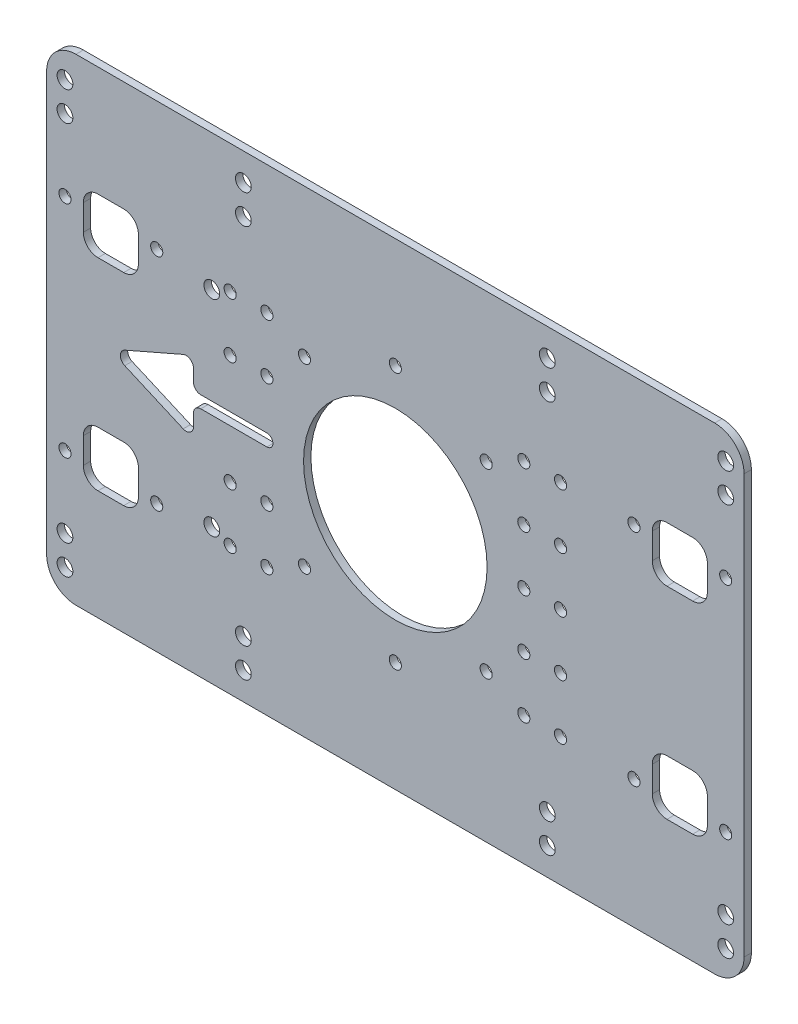
SolidWorks part; units mm, degrees
ref_plane "前视基准面" through (0, 0, 0) normal (0, 0, 1) x (1, 0, 0)
ref_plane "上视基准面" through (0, 0, 0) normal (0, 1, 0) x (1, 0, 0)
ref_plane "右视基准面" through (0, 0, 0) normal (1, 0, 0) x (0, 0, -1)
sketch "草图1" plane through (0, 0, 0) normal (0, 0, 1) x (1, 0, 0)
  line L0 (0, 65) -> (190, 65) construction
  line L1 (0, 0) -> (190, 0)
  line L2 (0, 0) -> (0, 130)
  line L3 (0, 130) -> (190, 130)
  line L4 (190, 0) -> (190, 130)
  line L5 (95, 130) -> (95, 0) construction
  line L6 (0, 0) -> (190, 0)
  line L7 (0, 130) -> (190, 130)
  circle A0 centre (5, 7.5) radius 2.15
  circle A1 centre (53.6, 7.5) radius 2.15
  circle A2 centre (53.6, 15.5) radius 2.15
  circle A3 centre (5, 15.5) radius 2.15
  circle A4 centre (5, 114.5) radius 2.15
  circle A5 centre (53.6, 122.5) radius 2.15
  circle A6 centre (5, 122.5) radius 2.15
  circle A7 centre (53.6, 114.5) radius 2.15
  circle A8 centre (53.6, 7.5) radius 2.15
  circle A9 centre (5, 7.5) radius 2.15
  circle A10 centre (5, 15.5) radius 2.15
  circle A11 centre (5, 114.5) radius 2.15
  circle A12 centre (53.6, 114.5) radius 2.15
  circle A13 centre (53.6, 122.5) radius 2.15
  circle A14 centre (5, 122.5) radius 2.15
  circle A15 centre (185, 122.5) radius 2.15
  circle A16 centre (136.4, 122.5) radius 2.15
  circle A17 centre (136.4, 114.5) radius 2.15
  circle A18 centre (185, 114.5) radius 2.15
  circle A19 centre (185, 15.5) radius 2.15
  circle A20 centre (185, 7.5) radius 2.15
  circle A21 centre (136.4, 7.5) radius 2.15
  circle A22 centre (136.4, 114.5) radius 2.15
  circle A23 centre (185, 122.5) radius 2.15
  circle A24 centre (136.4, 122.5) radius 2.15
  circle A25 centre (185, 114.5) radius 2.15
  circle A26 centre (185, 15.5) radius 2.15
  circle A27 centre (136.4, 15.5) radius 2.15
  circle A28 centre (136.4, 7.5) radius 2.15
  circle A29 centre (185, 7.5) radius 2.15
  dimension "D4" = 4.3
  dimension "D3" = 7.5
  dimension "D5" = 48.6
  dimension "D6" = 5
  dimension "D7" = 190
  dimension "D8" = 130
  dimension "D9" = 8
  dimension "D1" = 2
  dimension "D2" = 2
extrude "凸台-拉伸1" add sketch "草图1" along normal blind 2 contours L1 L4 L3 L2 A21 A19 A18 A17 A16 A15 A6 A4 A3 A2 A1 A0 A5 A7 A20 A27
fillet "圆角1" radius 8 4 edges at (0, 130, 1) (190, 130, 1) (190, 0, 1) (0, 0, 1)
sketch "草图2" plane through (0, 0, 0) normal (0, 0, -1) x (-1, 0, 0)
  line L0 (-95, 0) -> (-95, 130) construction
  line L1 (-190, 65) -> (0, 65) construction
  line L2 (-21, 85) -> (-14, 85)
  line L3 (-21, 30) -> (-14, 30)
  line L4 (0, 8) -> (0, 122)
  line L5 (-8, 130) -> (-182, 130)
  line L6 (-190, 122) -> (-190, 8)
  line L7 (-182, 0) -> (-8, 0)
  line L8 (0, 8) -> (0, 122)
  line L9 (-8, 130) -> (-182, 130)
  line L10 (-190, 122) -> (-190, 8)
  line L11 (-182, 0) -> (-8, 0)
  line L12 (-25, 34) -> (-25, 41)
  line L13 (-21, 45) -> (-14, 45)
  line L14 (-10, 34) -> (-10, 41)
  line L15 (-10, 96) -> (-10, 89)
  line L16 (-21, 100) -> (-14, 100)
  line L17 (-25, 96) -> (-25, 89)
  line L18 (-165, 96) -> (-165, 89)
  line L19 (-169, 100) -> (-176, 100)
  line L20 (-180, 96) -> (-180, 89)
  line L21 (-169, 85) -> (-176, 85)
  line L22 (-169, 45) -> (-176, 45)
  line L23 (-180, 34) -> (-180, 41)
  line L24 (-169, 30) -> (-176, 30)
  line L25 (-165, 34) -> (-165, 41)
  arc A0 (-14, 45) -> (-10, 41) centre (-14, 41) cw
  arc A1 (-25, 41) -> (-21, 45) centre (-21, 41) cw
  arc A2 (-10, 34) -> (-14, 30) centre (-14, 34) cw
  arc A3 (-21, 30) -> (-25, 34) centre (-21, 34) cw
  arc A4 (0, 122) -> (-8, 130) centre (-8, 122) ccw
  arc A5 (-182, 130) -> (-190, 122) centre (-182, 122) ccw
  arc A6 (-190, 8) -> (-182, 0) centre (-182, 8) ccw
  arc A7 (-8, 0) -> (0, 8) centre (-8, 8) ccw
  arc A8 (0, 122) -> (-8, 130) centre (-8, 122) ccw
  arc A9 (-182, 130) -> (-190, 122) centre (-182, 122) ccw
  arc A10 (-190, 8) -> (-182, 0) centre (-182, 8) ccw
  arc A11 (-8, 0) -> (0, 8) centre (-8, 8) ccw
  arc A12 (-14, 85) -> (-10, 89) centre (-14, 89) ccw
  arc A13 (-10, 96) -> (-14, 100) centre (-14, 96) ccw
  arc A14 (-25, 89) -> (-21, 85) centre (-21, 89) ccw
  arc A15 (-21, 100) -> (-25, 96) centre (-21, 96) ccw
  arc A16 (-165, 89) -> (-169, 85) centre (-169, 89) cw
  arc A17 (-169, 100) -> (-165, 96) centre (-169, 96) cw
  arc A18 (-180, 96) -> (-176, 100) centre (-176, 96) cw
  arc A19 (-176, 85) -> (-180, 89) centre (-176, 89) cw
  arc A20 (-176, 45) -> (-180, 41) centre (-176, 41) ccw
  arc A21 (-180, 34) -> (-176, 30) centre (-176, 34) ccw
  arc A22 (-165, 41) -> (-169, 45) centre (-169, 41) ccw
  arc A23 (-169, 30) -> (-165, 34) centre (-169, 34) ccw
  circle A24 centre (-95, 65) radius 25
  dimension "D2" = 4
  dimension "D7" = 50
  dimension "D3" = 15
  dimension "D4" = 15
  dimension "D5" = 30
  dimension "D6" = 10
  dimension "D8" = 0
  dimension "D1" = 0
extrude "切除-拉伸1" cut sketch "草图2" against normal blind 10 contours A24 | L12 A1 L13 A0 L14 A2 L3 A3 | L2 A12 L15 A13 L16 A15 L17 A14 | A16 L21 A19 L20 A18 L19 A17 L18 | L22 A20 L23 A21 L24 A23 L25 A22
sketch "草图4" plane through (0, 0, 0) normal (0, 0, -1) x (-1, 0, 0)
  line L0 (0, 65) -> (-60, 65)
  line L1 (-60, 65) -> (-40, 65) construction
  line L2 (-60, 66.65) -> (-40, 66.65)
  line L3 (-60, 63.35) -> (-40, 63.35)
  line L4 (0, 8) -> (0, 122)
  line L5 (-8, 130) -> (-182, 130)
  line L6 (-190, 122) -> (-190, 8)
  line L7 (-182, 0) -> (-8, 0)
  line L8 (0, 8) -> (0, 122)
  line L9 (-8, 130) -> (-182, 130)
  line L10 (-190, 122) -> (-190, 8)
  line L11 (-182, 0) -> (-8, 0)
  line L12 (-40, 75) -> (-40, 55)
  line L13 (-40, 55) -> (-17.0871, 65)
  line L14 (-40, 75) -> (-17.0871, 65)
  arc A0 (-60, 66.65) -> (-60, 63.35) centre (-60, 65) ccw
  arc A1 (-40, 63.35) -> (-40, 66.65) centre (-40, 65) ccw
  arc A4 (0, 122) -> (-8, 130) centre (-8, 122) ccw
  arc A5 (-182, 130) -> (-190, 122) centre (-182, 122) ccw
  arc A6 (-190, 8) -> (-182, 0) centre (-182, 8) ccw
  arc A7 (-8, 0) -> (0, 8) centre (-8, 8) ccw
  arc A8 (0, 122) -> (-8, 130) centre (-8, 122) ccw
  arc A9 (-182, 130) -> (-190, 122) centre (-182, 122) ccw
  arc A10 (-190, 8) -> (-182, 0) centre (-182, 8) ccw
  arc A11 (-8, 0) -> (0, 8) centre (-8, 8) ccw
  point P12 (-50, 65)
  point P22 (0, 0)
  point P25 (-40, 65)
  dimension "D3" = 1.65
  dimension "D2" = 20
  dimension "D4" = 10
  dimension "D5" = 25
  dimension "D7" = 60
  dimension "D1" = 0
extrude "切除-拉伸2" cut sketch "草图4" against normal blind 10
fillet "圆角2" radius 2 5 edges at (17.0871, 65, 1) (40, 63.35, 1) (40, 75, 1) (40, 55, 1) (40, 66.65, 1)
sketch "草图5" plane through (0, 0, 0) normal (0, 0, -1) x (-1, 0, 0)
  line L0 (-190, 65) -> (-129.7774, 65) construction
  line L4 (0, 8) -> (0, 122)
  line L5 (-8, 130) -> (-182, 130)
  line L6 (-190, 122) -> (-190, 8)
  line L7 (-182, 0) -> (-8, 0)
  line L8 (0, 8) -> (0, 122)
  line L9 (-8, 130) -> (-182, 130)
  line L10 (-190, 122) -> (-190, 8)
  line L11 (-182, 0) -> (-8, 0)
  circle A2 centre (-185, 35) radius 1.65
  circle A3 centre (-160, 35) radius 1.65
  arc A4 (0, 122) -> (-8, 130) centre (-8, 122) ccw
  arc A5 (-182, 130) -> (-190, 122) centre (-182, 122) ccw
  arc A6 (-190, 8) -> (-182, 0) centre (-182, 8) ccw
  arc A7 (-8, 0) -> (0, 8) centre (-8, 8) ccw
  arc A8 (0, 122) -> (-8, 130) centre (-8, 122) ccw
  arc A9 (-182, 130) -> (-190, 122) centre (-182, 122) ccw
  arc A10 (-190, 8) -> (-182, 0) centre (-182, 8) ccw
  arc A11 (-8, 0) -> (0, 8) centre (-8, 8) ccw
  circle A12 centre (-160, 95) radius 1.65
  circle A13 centre (-185, 95) radius 1.65
  point P22 (0, 0)
  dimension "D2" = 3.3
  dimension "D3" = 30
  dimension "D4" = 5
  dimension "D5" = 2
  dimension "D1" = 0
extrude "切除-拉伸5" cut sketch "草图5" against normal blind 3.3 contours A3 | A13 | A2 | A12
ref_plane "基准面1" through (95, 0, 0) normal (-1, 0, 0) x (0, 0, 1)
sketch "草图6" plane through (0, 0, 0) normal (0, 0, -1) x (-1, 0, 0)
  line L0 (-190, 65) -> (-120, 65) construction
  line L4 (0, 8) -> (0, 122)
  line L5 (-8, 130) -> (-182, 130)
  line L6 (-190, 122) -> (-190, 8)
  line L7 (-182, 0) -> (-8, 0)
  line L8 (0, 8) -> (0, 122)
  line L9 (-8, 130) -> (-182, 130)
  line L10 (-190, 122) -> (-190, 8)
  line L11 (-182, 0) -> (-8, 0)
  circle A0 centre (-95, 65) radius 25 construction
  circle A1 centre (-140, 35) radius 1.65
  circle A2 centre (-130, 35) radius 1.65
  circle A3 centre (-130, 50) radius 1.65
  arc A4 (0, 122) -> (-8, 130) centre (-8, 122) ccw
  arc A5 (-182, 130) -> (-190, 122) centre (-182, 122) ccw
  arc A6 (-190, 8) -> (-182, 0) centre (-182, 8) ccw
  arc A7 (-8, 0) -> (0, 8) centre (-8, 8) ccw
  arc A8 (0, 122) -> (-8, 130) centre (-8, 122) ccw
  arc A9 (-182, 130) -> (-190, 122) centre (-182, 122) ccw
  arc A10 (-190, 8) -> (-182, 0) centre (-182, 8) ccw
  arc A11 (-8, 0) -> (0, 8) centre (-8, 8) ccw
  circle A12 centre (-130, 65) radius 1.65
  circle A13 centre (-130, 80) radius 1.65
  circle A14 centre (-130, 95) radius 1.65
  circle A15 centre (-140, 50) radius 1.65
  circle A16 centre (-140, 65) radius 1.65
  circle A17 centre (-140, 80) radius 1.65
  circle A18 centre (-140, 95) radius 1.65
  circle A19 centre (-95, 65) radius 25 construction
  circle A20 centre (-95, 65) radius 25
  circle A21 centre (-95, 30) radius 1.65
  circle A22 centre (-119.7487, 40.2513) radius 1.65
  circle A23 centre (-130, 65) radius 1.65
  circle A24 centre (-119.7487, 89.7487) radius 1.65
  circle A25 centre (-95, 100) radius 1.65
  circle A26 centre (-70.2513, 89.7487) radius 1.65
  circle A27 centre (-60, 65) radius 1.65
  circle A28 centre (-70.2513, 40.2513) radius 1.65
  point P59 (-95, 65)
  dimension "D2" = 3.3
  dimension "D7" = 3.3
  dimension "D3" = 50
  dimension "D4" = 30
  dimension "D8" = 35
  dimension "D1" = 0
  dimension "D5" = 2
  dimension "D6" = 5
  dimension "D9" = 8
extrude "切除-拉伸6" cut sketch "草图6" against normal blind 3.3 contours A1 | A15 | A16 | A17 | A18 | A14 | A13 | A12 | A3 | A2 | A22 | A24 | A25 | A26 | A28 | A21
mirror "镜向1" about plane through (95, 0, 0) normal (-1, 0, 0) of "切除-拉伸6"
mirror "镜向2" about plane through (95, 0, 0) normal (-1, 0, 0) of "切除-拉伸5"
sketch "草图7" plane through (0, 0, 2) normal (0, 0, 1) x (1, 0, 0)
  line L0 (20.0871, 65) -> (61.65, 65) construction
  line L4 (182, 130) -> (8, 130)
  line L5 (0, 122) -> (0, 8)
  line L6 (8, 0) -> (182, 0)
  line L7 (190, 8) -> (190, 122)
  line L8 (182, 130) -> (8, 130)
  line L9 (0, 122) -> (0, 8)
  line L10 (8, 0) -> (182, 0)
  line L11 (190, 8) -> (190, 122)
  arc A0 (21.2871, 66.833) -> (21.2871, 63.167) centre (22.0871, 65) ccw construction
  arc A1 (60, 63.35) -> (60, 66.65) centre (60, 65) ccw construction
  circle A2 centre (45, 37) radius 2.15
  circle A3 centre (45, 93) radius 2.15
  arc A4 (8, 130) -> (0, 122) centre (8, 122) ccw
  arc A5 (0, 8) -> (8, 0) centre (8, 8) ccw
  arc A6 (182, 0) -> (190, 8) centre (182, 8) ccw
  arc A7 (190, 122) -> (182, 130) centre (182, 122) ccw
  arc A8 (8, 130) -> (0, 122) centre (8, 122) ccw
  arc A9 (0, 8) -> (8, 0) centre (8, 8) ccw
  arc A10 (182, 0) -> (190, 8) centre (182, 8) ccw
  arc A11 (190, 122) -> (182, 130) centre (182, 122) ccw
  dimension "D2" = 4.3
  dimension "D3" = 28
  dimension "D4" = 45
  dimension "D1" = 0
extrude "切除-拉伸7" cut sketch "草图7" against normal blind 3.3 contours A3 | A2
